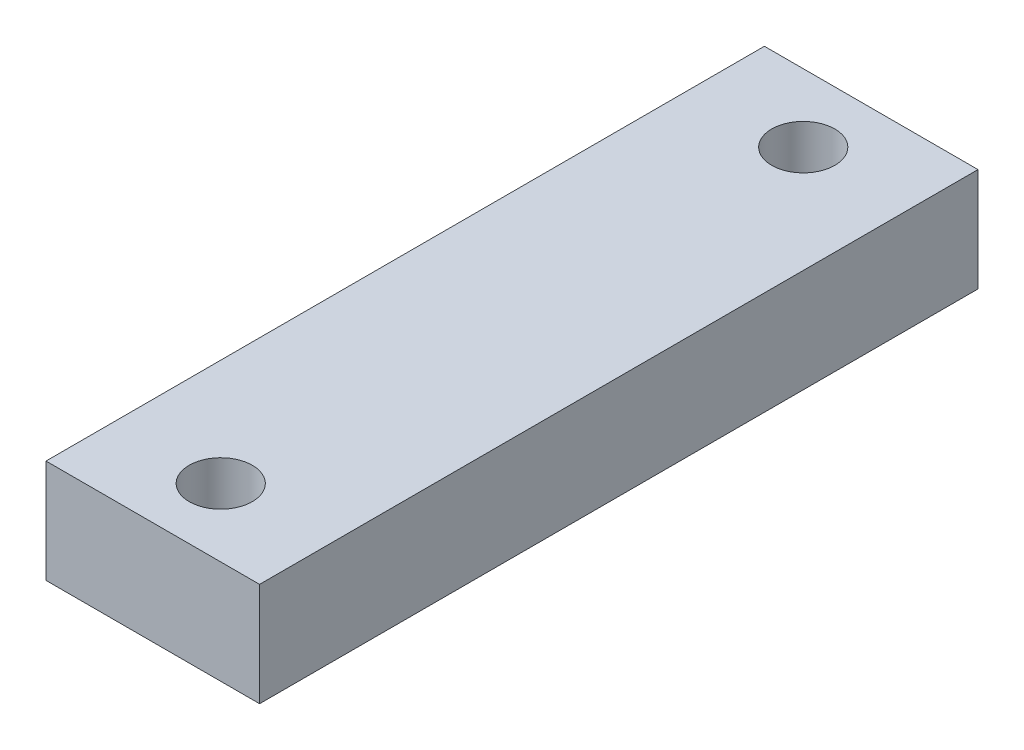
SolidWorks part; units mm, degrees
ref_plane "Alzado" through (0, 0, 0) normal (0, 0, 1) x (1, 0, 0)
ref_plane "Planta" through (0, 0, 0) normal (0, 1, 0) x (1, 0, 0)
ref_plane "Vista lateral" through (0, 0, 0) normal (1, 0, 0) x (0, 0, -1)
sketch "Croquis1" plane through (0, 0, 0) normal (0, 0, 1) x (1, 0, 0)
  line L3 (29, -5.325) -> (29, 5.325)
  line L4 (29, 5.325) -> (7, 5.325)
  line L6 (29, -5.325) -> (7, -5.325)
  line L7 (7, -5.325) -> (7, 5.325)
  dimension "D1" = 22
  dimension "D2" = 10.65
extrude "Saliente-Extruir1" add sketch "Croquis1" along normal blind 74
sketch "Croquis2" plane through (0, 5.325, 0) normal (0, 1, 0) x (1, 0, 0)
  line L0 (7, -74) -> (7, 0) construction
  line L1 (29, 0) -> (7, 0) construction
  circle A0 centre (18, -7) radius 3.25
  circle A1 centre (18, -67) radius 3.25
  dimension "D1" = 11
  dimension "D2" = 7
  dimension "D3" = 6.5
  dimension "D4" = 60
extrude "Cortar-Extruir1" cut sketch "Croquis2" against normal up to next
